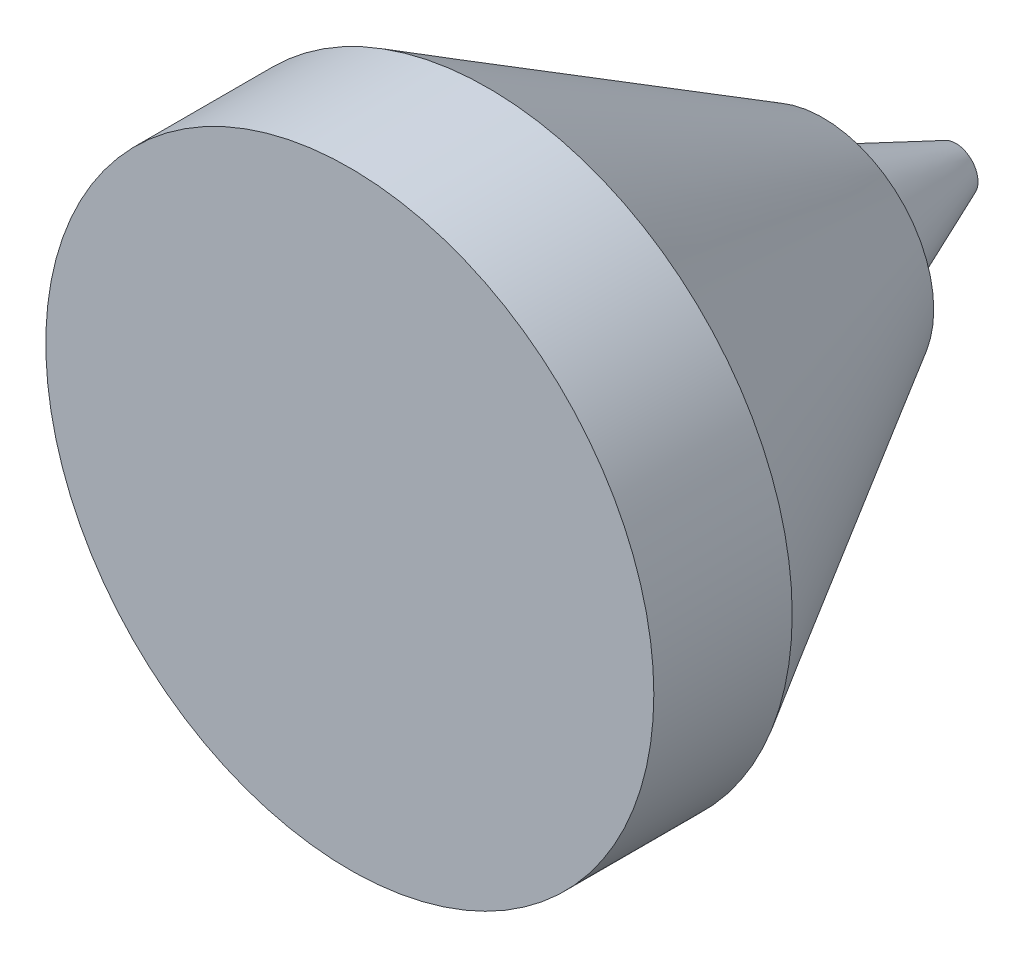
SolidWorks part; units mm, degrees
ref_plane "Plan de face" through (0, 0, 0) normal (0, 0, 1) x (1, 0, 0)
ref_plane "Plan de dessus" through (0, 0, 0) normal (0, 1, 0) x (1, 0, 0)
ref_plane "Plan de droite" through (0, 0, 0) normal (1, 0, 0) x (0, 0, -1)
sketch "Esquisse1" plane through (0, 0, 0) normal (1, 0, 0) x (0, 0, -1)
  line L0 (-35.55, 0) -> (35.55, 0) construction
  line L1 (-30.55, 10.9859) -> (-35.55, 10.9859)
  line L2 (-35.55, 10.9859) -> (-35.55, 0)
  line L3 (-30.55, 10.9859) -> (-18.45, 4)
  line L4 (-18.45, 4) -> (30.55, 15.4)
  line L5 (30.55, 15.4) -> (35.55, 15.4)
  line L10 (35.55, 15.4) -> (35.55, 0)
  line L11 (-35.55, 0) -> (35.55, 0)
  line L13 (-35.55, 0) -> (35.55, 0) construction
  dimension "D1" = 12.1
  dimension "D2" = 49
  dimension "D3" = 15.4
  dimension "D4" = 8
  dimension "D5" = 30
  dimension "D6" = 5
  dimension "D7" = 5
revolve "Révolution1" add sketch "Esquisse1" angle 360 about L11
ref_plane "Plan1" through (0, 0, 18.45) normal (0, 0, 1) x (1, 0, 0)
sketch "Esquisse2" plane through (0, 0, 18.45) normal (0, 0, 1) x (1, 0, 0)
  circle A0 centre (0, 0) radius 15.4
  circle A1 centre (0, 0) radius 15.4 construction
extrude "Enlèv. mat.-Extru.1" cut sketch "Esquisse2" against normal up to surface (54 mm away) up to face at (15.4, 0, -35.55)
sketch "Esquisse6" plane through (0, 0, 0) normal (1, 0, 0) x (0, 0, -1)
  line L0 (-18.45, 2.8) -> (-13.65, 0.8)
  line L2 (-13.65, 0.8) -> (-13.65, 0)
  line L3 (-13.65, 0) -> (-18.45, 0) construction
  line L5 (-18.45, 2.8) -> (-18.45, 0)
  line L6 (-13.65, 0) -> (-18.45, 0)
  line L7 (-18.45, -4) -> (-18.45, 4) construction
  dimension "D1" = 2.8
  dimension "D2" = 0.8
  dimension "D3" = 4.8
revolve "Révolution2" add sketch "Esquisse6" angle 360 about L3
sketch "Esquisse4" [suppressed] plane through (0, 0, 18.45) normal (0, 0, 1) x (1, 0, 0)
  circle A0 centre (0, 0) radius 10.9859
  circle A1 centre (0, 0) radius 10.9859 construction
extrude "Enlèv. mat.-Extru.2" [suppressed] cut sketch "Esquisse4" along normal up to surface (17.1 mm away)
sketch "Esquisse7" [suppressed] plane through (0, 0, 0) normal (1, 0, 0) x (0, 0, -1)
  line L0 (-18.45, 0) -> (-18.45, 3)
  line L1 (-18.45, 4) -> (-18.45, -4) construction
  line L2 (-18.45, 3) -> (-13.45, 1)
  line L3 (-13.45, 1) -> (-13.45, 0)
  line L4 (-18.45, 0) -> (-13.45, 0)
  dimension "D1" = 5
  dimension "D2" = 1
  dimension "D3" = 3
revolve "Enlèvement de matière-Révolution1" [suppressed] cut sketch "Esquisse7" angle 360 about L4
